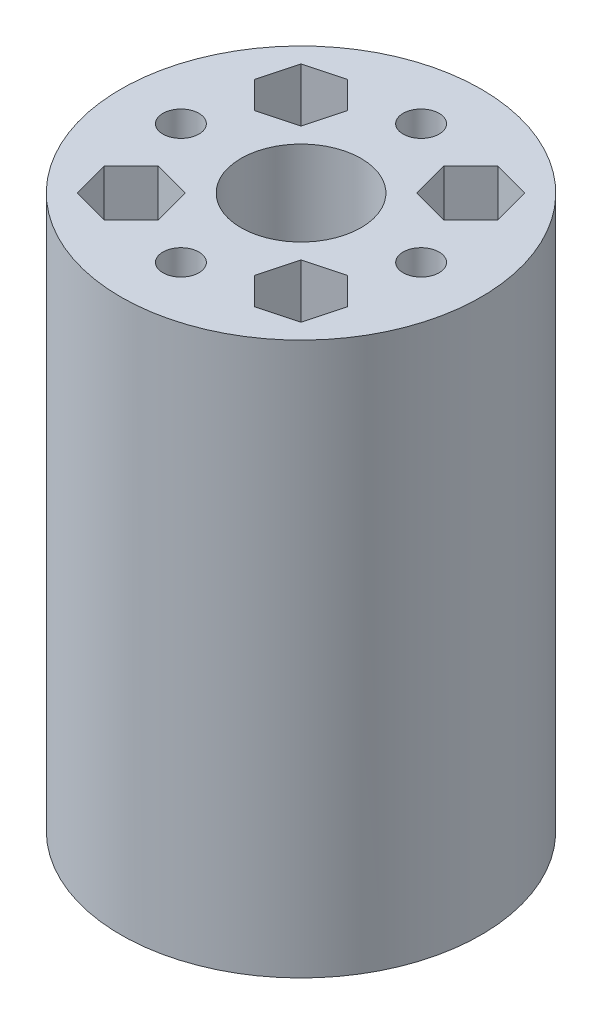
SolidWorks part; units mm, degrees
ref_plane "前视基准面" through (0, 0, 0) normal (0, 0, 1) x (1, 0, 0)
ref_plane "上视基准面" through (0, 0, 0) normal (0, 1, 0) x (1, 0, 0)
ref_plane "右视基准面" through (0, 0, 0) normal (1, 0, 0) x (0, 0, -1)
sketch "草图1" plane through (0, 0, 0) normal (0, 1, 0) x (1, 0, 0)
  circle A0 centre (-5.3729, -8.9317) radius 15
  circle A1 centre (-22.3729, 8.0683) radius 2.1
  circle A5 centre (-5.3729, -8.9317) radius 5
  circle A6 centre (-22.3729, 8.0683) radius 3.5
  dimension "D4" = 4.2
  dimension "D8" = 10
  dimension "D9" = 7
extrude "凸台-拉伸4" add sketch "草图1" along normal blind 3
sketch "草图5" plane through (0, 0, 0) normal (0, 1, 0) x (1, 0, 0)
  line L0 (-22.3729, 4.5683) -> (-10.3729, -8.9317)
  line L1 (-5.3729, -3.9317) -> (-18.8729, 8.0683)
  line L2 (-18.8729, 8.0683) -> (-22.3729, 4.5683)
  line L3 (-10.3729, -8.9317) -> (-10.3729, -3.9317)
  line L4 (-10.3729, -3.9317) -> (-5.3729, -3.9317)
  circle A0 centre (-22.3729, 8.0683) radius 3.5 construction
  circle A1 centre (-5.3729, -8.9317) radius 5 construction
extrude "凸台-拉伸5" add sketch "草图5" along normal blind 3
pattern_circular "阵列(圆周)2" count 4 over 360 about axis through (-5.3729, 0, 8.9317) along (0, 1, 0) of "凸台-拉伸5"
sketch "草图6" plane through (0, 3, 0) normal (0, 1, 0) x (1, 0, 0)
  circle A0 centre (11.6271, 8.0683) radius 2.1
  circle A1 centre (11.6271, 8.0683) radius 3.5
  dimension "D2" = 4.2
  dimension "D3" = 7
extrude "凸台-拉伸6" add sketch "草图6" against normal blind 3
pattern_circular "阵列(圆周)3" count 4 over 360 about axis through (-5.3729, 0, 8.9317) along (0, 1, 0) of "凸台-拉伸6"
sketch "草图7" plane through (0, 0, 0) normal (0, -1, 0) x (1, 0, 0)
  circle A0 centre (-5.3729, 8.9317) radius 15
  circle A1 centre (-5.3729, 8.9317) radius 5
extrude "凸台-拉伸7" add sketch "草图7" along normal blind 46
sketch "草图8" plane through (0, -46, 0) normal (0, -1, 0) x (1, 0, 0)
  line L4 (3.9435, 18.2482) -> (0.8763, 19.07)
  line L5 (0.8763, 19.07) -> (-1.3691, 16.8247)
  line L6 (-1.3691, 16.8247) -> (-0.5472, 13.7574)
  line L7 (-0.5472, 13.7574) -> (2.52, 12.9356)
  line L8 (2.52, 12.9356) -> (4.7654, 15.1809)
  line L9 (4.7654, 15.1809) -> (3.9435, 18.2482)
  circle A3 centre (1.6982, 16.0028) radius 2.75 construction
  dimension "D1" = 5.5
sketch "草图9" plane through (0, 3, 0) normal (0, 1, 0) x (1, 0, 0)
  line L0 (0.8763, -19.07) -> (-1.3691, -16.8247) construction
  line L1 (3.9435, -18.2482) -> (0.8763, -19.07) construction
  line L2 (4.7654, -15.1809) -> (3.9435, -18.2482) construction
  line L3 (2.52, -12.9356) -> (4.7654, -15.1809) construction
  line L4 (-0.5472, -13.7574) -> (2.52, -12.9356) construction
  line L5 (-1.3691, -16.8247) -> (-0.5472, -13.7574) construction
  line L6 (0.8763, -19.07) -> (-1.3691, -16.8247)
  line L7 (3.9435, -18.2482) -> (0.8763, -19.07)
  line L8 (4.7654, -15.1809) -> (3.9435, -18.2482)
  line L9 (2.52, -12.9356) -> (4.7654, -15.1809)
  line L10 (-0.5472, -13.7574) -> (2.52, -12.9356)
  line L11 (-1.3691, -16.8247) -> (-0.5472, -13.7574)
extrude "切除-拉伸1" cut sketch "草图9" against normal blind 46
pattern_circular "阵列(圆周)4" count 4 over 360 about axis through (-5.3729, 0, 8.9317) along (0, 1, 0) of "切除-拉伸1"
sketch "草图11" plane through (0, -43, 0) normal (0, 1, 0) x (1, 0, 0)
  circle A0 centre (1.6982, -1.8607) radius 1.5
  dimension "D1" = 3
extrude "切除-拉伸2" cut sketch "草图11" against normal blind 3
pattern_circular "阵列(圆周)5" count 4 over 360 about axis through (-5.3729, 0, 8.9317) along (0, 1, 0) of "切除-拉伸2"
sketch "草图12" plane through (0, 3, 0) normal (0, 1, 0) x (1, 0, 0)
  line L0 (15.1271, 8.0683) -> (15.1271, -25.9317)
  line L1 (15.1271, -25.9317) -> (11.6271, -22.4317)
  line L2 (11.6271, -22.4317) -> (11.6271, 4.5683)
  line L3 (11.6271, 4.5683) -> (15.1271, 8.0683)
  arc A0 (11.6271, 4.5683) -> (8.1271, 8.0683) centre (11.6271, 8.0683) ccw construction
  arc A1 (8.1271, -25.9317) -> (11.6271, -22.4317) centre (11.6271, -25.9317) ccw construction
extrude "凸台-拉伸8" add sketch "草图12" against normal blind 3
sketch "草图13" plane through (0, 3, 0) normal (0, 1, 0) x (1, 0, 0)
  line L0 (11.6271, 11.5683) -> (-22.3729, 11.5683)
  line L1 (-22.3729, 11.5683) -> (-18.8729, 8.0683)
  line L2 (-18.8729, 8.0683) -> (8.1271, 8.0683)
  line L3 (8.1271, 8.0683) -> (11.6271, 11.5683)
  arc A0 (15.1271, 8.0683) -> (8.1271, 8.0683) centre (11.6271, 8.0683) ccw construction
  arc A1 (-18.8729, 8.0683) -> (-22.3729, 4.5683) centre (-22.3729, 8.0683) ccw construction
extrude "凸台-拉伸9" add sketch "草图13" against normal blind 3
sketch "草图14" plane through (0, 3, 0) normal (0, 1, 0) x (1, 0, 0)
  line L0 (-25.8729, 8.0683) -> (-25.8729, -25.9317)
  line L1 (-25.8729, -25.9317) -> (-22.3729, -22.4317)
  line L2 (-22.3729, -22.4317) -> (-22.3729, 4.5683)
  line L3 (-22.3729, 4.5683) -> (-25.8729, 8.0683)
  arc A0 (-22.3729, 11.5683) -> (-22.3729, 4.5683) centre (-22.3729, 8.0683) ccw construction
  arc A1 (-22.3729, -22.4317) -> (-18.8729, -25.9317) centre (-22.3729, -25.9317) ccw construction
extrude "凸台-拉伸10" add sketch "草图14" against normal blind 3
sketch "草图15" plane through (0, 3, 0) normal (0, 1, 0) x (1, 0, 0)
  line L0 (-22.3729, -29.4317) -> (11.6271, -29.4317)
  line L1 (11.6271, -29.4317) -> (8.1271, -25.9317)
  line L2 (8.1271, -25.9317) -> (-18.8729, -25.9317)
  line L3 (-18.8729, -25.9317) -> (-22.3729, -29.4317)
  arc A0 (-25.8729, -25.9317) -> (-18.8729, -25.9317) centre (-22.3729, -25.9317) ccw construction
  arc A1 (8.1271, -25.9317) -> (15.1271, -25.9317) centre (11.6271, -25.9317) ccw construction
extrude "凸台-拉伸11" add sketch "草图15" against normal blind 3
sketch "草图16" plane through (0, 0, 0) normal (0, -1, 0) x (1, 0, 0)
  line L0 (-10.7479, -4.1933) -> (0.0021, -4.1933)
  line L1 (0.0021, -4.1933) -> (5.1636, -8.0683)
  line L2 (-18.8729, -8.0683) -> (8.1271, -8.0683) construction
  line L3 (4.9912, -11.5683) -> (0.0021, -14.9433)
  line L4 (11.6271, -11.5683) -> (-22.3729, -11.5683) construction
  line L5 (-7.5725, -9.5683) -> (-9.1602, -6.8183)
  line L6 (-9.1602, -6.8183) -> (-12.3356, -6.8183)
  line L7 (-12.3356, -6.8183) -> (-13.9233, -9.5683)
  line L8 (-13.9233, -9.5683) -> (-12.3356, -12.3183)
  line L9 (-12.3356, -12.3183) -> (-9.1602, -12.3183)
  line L10 (-9.1602, -12.3183) -> (-7.5725, -9.5683)
  line L11 (3.1775, -9.5683) -> (1.5898, -6.8183)
  line L12 (1.5898, -6.8183) -> (-1.5856, -6.8183)
  line L13 (-1.5856, -6.8183) -> (-3.1733, -9.5683)
  line L14 (-3.1733, -9.5683) -> (-1.5856, -12.3183)
  line L15 (-1.5856, -12.3183) -> (1.5898, -12.3183)
  line L16 (1.5898, -12.3183) -> (3.1775, -9.5683)
  line L17 (0.0021, -14.9433) -> (-10.7479, -14.9433)
  line L18 (-10.7479, -14.9433) -> (-15.7369, -11.5683)
  line L19 (-15.7369, -11.5683) -> (-15.9094, -8.0683)
  line L20 (-15.9094, -8.0683) -> (-10.7479, -4.1933)
  line L21 (4.9912, -11.5683) -> (5.1636, -8.0683)
  circle A0 centre (-10.7479, -9.5683) radius 2.75 construction
  circle A2 centre (0.0021, -9.5683) radius 2.75 construction
  dimension "D4" = 5.5
  dimension "D5" = 5.5
sketch "草图17" plane through (0, 0, 0) normal (0, -1, 0) x (1, 0, 0)
  line L1 (-7.5725, -9.5683) -> (-9.1602, -6.8183)
  line L2 (-9.1602, -6.8183) -> (-12.3356, -6.8183)
  line L3 (-12.3356, -6.8183) -> (-13.9233, -9.5683)
  line L4 (-13.9233, -9.5683) -> (-12.3356, -12.3183)
  line L5 (-12.3356, -12.3183) -> (-9.1602, -12.3183)
  line L6 (-9.1602, -12.3183) -> (-7.5725, -9.5683)
  line L7 (3.1775, -9.5683) -> (1.5898, -6.8183)
  line L8 (1.5898, -6.8183) -> (-1.5856, -6.8183)
  line L9 (-1.5856, -6.8183) -> (-3.1733, -9.5683)
  line L10 (-3.1733, -9.5683) -> (-1.5856, -12.3183)
  line L11 (-1.5856, -12.3183) -> (1.5898, -12.3183)
  line L12 (1.5898, -12.3183) -> (3.1775, -9.5683)
  circle A0 centre (-10.7479, -9.5683) radius 2.75 construction
  circle A1 centre (0.0021, -9.5683) radius 2.75 construction
extrude "凸台-拉伸13" add sketch "草图16" against normal blind 3
sketch "草图18" plane through (0, 0, 0) normal (0, -1, 0) x (1, 0, 0)
  line L1 (-7.5725, -9.5683) -> (-9.1602, -6.8183)
  line L2 (-9.1602, -6.8183) -> (-12.3356, -6.8183)
  line L3 (-12.3356, -6.8183) -> (-13.9233, -9.5683)
  line L4 (-13.9233, -9.5683) -> (-12.3356, -12.3183)
  line L5 (-12.3356, -12.3183) -> (-9.1602, -12.3183)
  line L6 (-9.1602, -12.3183) -> (-7.5725, -9.5683)
  line L7 (3.1775, -9.5683) -> (1.5898, -6.8183)
  line L8 (1.5898, -6.8183) -> (-1.5856, -6.8183)
  line L9 (-1.5856, -6.8183) -> (-3.1733, -9.5683)
  line L10 (-3.1733, -9.5683) -> (-1.5856, -12.3183)
  line L11 (-1.5856, -12.3183) -> (1.5898, -12.3183)
  line L12 (1.5898, -12.3183) -> (3.1775, -9.5683)
  circle A0 centre (-10.7479, -9.5683) radius 2.75 construction
  circle A1 centre (0.0021, -9.5683) radius 2.75 construction
extrude "凸台-拉伸14" add sketch "草图18" against normal blind 3
extrude "切除-拉伸3" cut sketch "草图17" against normal blind 2.5
sketch "草图19" plane through (0, 2.5, 0) normal (0, -1, 0) x (1, 0, 0)
  circle A0 centre (0.0021, -9.5683) radius 1.5
  dimension "D1" = 3
extrude "切除-拉伸4" cut sketch "草图19" against normal blind 2.5
sketch "草图20" plane through (0, 2.5, 0) normal (0, -1, 0) x (1, 0, 0)
  circle A0 centre (-10.7479, -9.5683) radius 1.5
  dimension "D1" = 3
extrude "切除-拉伸5" cut sketch "草图20" against normal blind 2.5
sketch "草图21" plane through (0, 0, 0) normal (0, 1, 0) x (1, 0, 0)
  circle A0 centre (59.6655, -8.9317) radius 15
  circle A1 centre (59.6655, -8.9317) radius 5
  dimension "D1" = 30
  dimension "D2" = 10
extrude "凸台-拉伸15" add sketch "草图21" along normal blind 3 separate body
sketch "草图22" plane through (0, 0, 0) normal (0, -1, 0) x (1, 0, 0)
  circle A0 centre (59.6655, 18.9317) radius 1.5
  dimension "D2" = 3
extrude "切除-拉伸6" cut sketch "草图22" against normal blind 3
pattern_circular "阵列(圆周)6" count 4 over 360 about axis through (59.6655, 0, 8.9317) along (0, 1, 0) of "切除-拉伸6"
extrude "凸台-拉伸16" add sketch "草图8" along normal blind 3
sketch "草图24" plane through (0, -49, 0) normal (0, -1, 0) x (1, 0, 0)
  line L1 (4.7654, 15.1809) -> (3.9435, 18.2482)
  line L2 (3.9435, 18.2482) -> (0.8763, 19.07)
  line L3 (0.8763, 19.07) -> (-1.3691, 16.8247)
  line L4 (-1.3691, 16.8247) -> (-0.5472, 13.7574)
  line L5 (-0.5472, 13.7574) -> (2.52, 12.9356)
  line L6 (2.52, 12.9356) -> (4.7654, 15.1809)
  circle A0 centre (1.6982, 16.0028) radius 2.75 construction
extrude "切除-拉伸7" cut sketch "草图24" against normal blind 3
sketch "草图25" plane through (0, 0, 0) normal (0, -1, 0) x (1, 0, 0)
  circle A0 centre (59.6655, 8.9317) radius 15
  circle A1 centre (59.6655, 8.9317) radius 5
extrude "凸台-拉伸17" add sketch "草图25" along normal blind 43
sketch "草图27" plane through (0, 3, 0) normal (0, 1, 0) x (1, 0, 0)
  circle A0 centre (59.6655, 1.0683) radius 1.5
  circle A1 centre (69.6655, -8.9317) radius 1.5
  circle A2 centre (59.6655, -18.9317) radius 1.5
  circle A3 centre (49.6655, -8.9317) radius 1.5
extrude "切除-拉伸8" cut sketch "草图27" against normal blind 46
sketch "草图28" plane through (0, -43, 0) normal (0, -1, 0) x (1, 0, 0)
  circle A0 centre (59.6655, 18.9317) radius 2.75
  circle A1 centre (49.6655, 8.9317) radius 2.75
  circle A2 centre (59.6655, -1.0683) radius 2.75
  circle A3 centre (69.6655, 8.9317) radius 2.75
  dimension "D1" = 5.5
  dimension "D2" = 5.5
  dimension "D3" = 5.5
  dimension "D4" = 5.5
extrude "切除-拉伸9" cut sketch "草图28" against normal blind 43
sketch "草图29" plane through (0, 3, 0) normal (0, 1, 0) x (1, 0, 0)
  circle A0 centre (66.7366, -1.8607) radius 1.5
  dimension "D2" = 3
extrude "切除-拉伸10" cut sketch "草图29" against normal blind 46
pattern_circular "阵列(圆周)7" count 4 over 360 about axis through (59.6655, 0, 8.9317) along (0, 1, 0) of "切除-拉伸10"
sketch "草图30" plane through (0, 3, 0) normal (0, 1, 0) x (1, 0, 0)
  line L2 (64.4912, -4.106) -> (67.5585, -4.9279)
  line L3 (67.5585, -4.9279) -> (69.8038, -2.6825)
  line L4 (69.8038, -2.6825) -> (68.982, 0.3847)
  line L5 (68.982, 0.3847) -> (65.9148, 1.2066)
  line L6 (65.9148, 1.2066) -> (63.6694, -1.0388)
  line L7 (63.6694, -1.0388) -> (64.4912, -4.106)
  circle A0 centre (66.7366, -1.8607) radius 2.75 construction
  dimension "D1" = 5.5
extrude "切除-拉伸11" cut sketch "草图30" against normal blind 43
pattern_circular "阵列(圆周)8" count 4 over 360 about axis through (59.6655, 0, 8.9317) along (0, 1, 0) of "切除-拉伸11"
sketch "草图31" plane through (0, 3, 0) normal (0, 1, 0) x (1, 0, 0)
  circle A0 centre (-6.8653, -8.3724) radius 43.8557
extrude "切除-拉伸12" cut sketch "草图31" against normal blind 100
